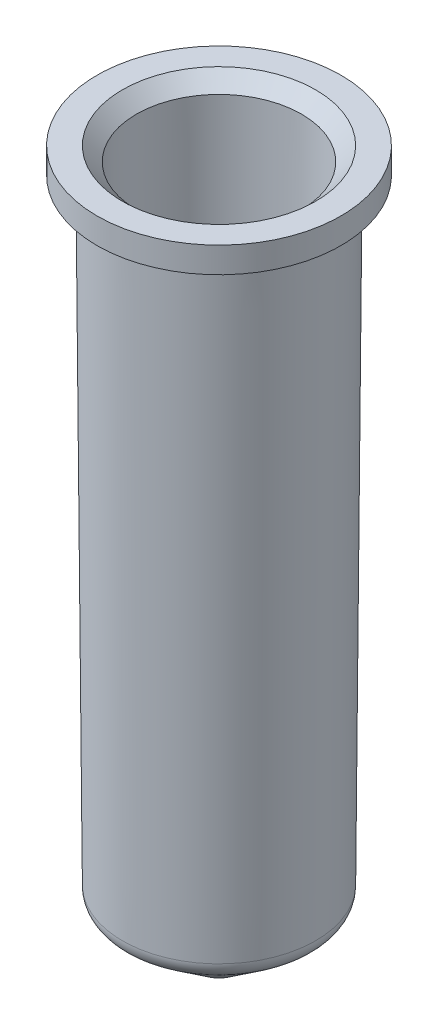
SolidWorks part; units mm, degrees
ref_plane "Front Plane" through (0, 0, 0) normal (0, 0, 1) x (1, 0, 0)
ref_plane "Top Plane" through (0, 0, 0) normal (0, 1, 0) x (1, 0, 0)
ref_plane "Right Plane" through (0, 0, 0) normal (1, 0, 0) x (0, 0, -1)
sketch "Sketch1" plane through (0, 0, 0) normal (0, 0, 1) x (1, 0, 0)
  line L0 (0, 0) -> (0, 36.0603) construction
  line L1 (1.1973, -3.458) -> (4.7524, -0.801)
  line L2 (5.1537, -0.0075) -> (5.4, 32.774)
  line L3 (4.1538, 0) -> (4.4046, 33.394)
  line L4 (0.5986, -2.657) -> (4.1538, 0)
  line L5 (5.1546, 34.144) -> (6.5046, 34.144)
  line L6 (6.5046, 34.144) -> (6.5046, 32.774)
  line L7 (6.5046, 32.774) -> (5.4, 32.774)
  line L8 (5.1537, -0.0075) -> (5.4179, 35.1598) construction
  line L9 (4.1538, 0) -> (4.418, 35.1674) construction
  line L10 (4.4046, 33.394) -> (5.1546, 34.144)
  line L11 (0, -3.856) -> (0, -2.856)
  arc A0 (1.1973, -3.458) -> (0, -3.856) centre (0, -1.856) cw
  arc A1 (4.7524, -0.801) -> (5.1537, -0.0075) centre (4.1538, 0) ccw
  arc A2 (4.1538, 0) -> (4.1538, 0) centre (4.1538, 0) ccw
  arc A3 (0.5986, -2.657) -> (0, -2.856) centre (0, -1.856) cw
  point P9 (0, -2.3188)
  point P10 (0.6309, -3.7539)
  point P13 (5.15, -0.5039)
  dimension "D3" = 2
  dimension "D5" = 1
  dimension "D1" = 5.15
  dimension "D2" = 1.37
  dimension "D4" = 3.25
  dimension "D7" = 5.4
  dimension "D8" = 38
  dimension "D9" = 2.1
  dimension "D10" = 135
  dimension "D11" = 0.75
  dimension "D6" = 1
revolve "Revolve1" add sketch "Sketch1" angle 360 about L0
